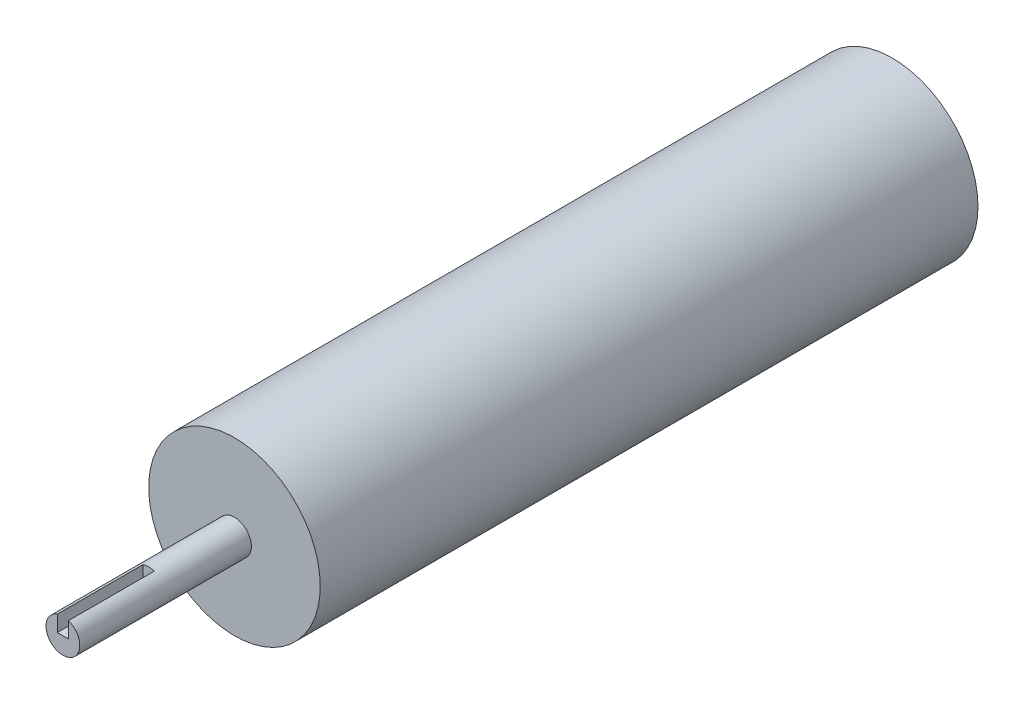
SolidWorks part; units mm, degrees
ref_plane "Front Plane" through (0, 0, 0) normal (0, 0, 1) x (1, 0, 0)
ref_plane "Top Plane" through (0, 0, 0) normal (0, 1, 0) x (1, 0, 0)
ref_plane "Right Plane" through (0, 0, 0) normal (1, 0, 0) x (0, 0, -1)
sketch "Sketch1" plane through (0, 0, 0) normal (0, 0, 1) x (1, 0, 0)
  circle A1 centre (0, 0) radius 38.1
  dimension "D2" = 76.2
extrude "Boss-Extrude1" add sketch "Sketch1" along normal blind 292.1
sketch "Sketch3" plane through (0, 0, 292.1) normal (0, 0, 1) x (1, 0, 0)
  line L0 (0, 38.1) -> (0, -38.1) construction
  line L1 (-38.1, 0) -> (38.1, 0) construction
  circle A0 centre (0, 0) radius 7.5
  circle A1 centre (0, 0) radius 38.1 construction
  dimension "D1" = 15
extrude "Boss-Extrude2" add sketch "Sketch3" along normal blind 76.2
sketch "Sketch4" plane through (0, 0, 368.3) normal (0, 0, 1) x (1, 0, 0)
  line L1 (-2.5, 0) -> (2.5, 0)
  line L2 (-2.5, 0) -> (-2.5, 7.0711)
  line L3 (2.5, 0) -> (2.5, 7.0711)
  circle A1 centre (0, 0) radius 7.5 construction
  point P10 (0, 0)
  dimension "D1" = 5
extrude "Cut-Extrude1" cut sketch "Sketch4" against normal blind 38.1 and the other way through all
sketch "Sketch5" plane through (0, 0, 0) normal (0, 0, -1) x (-1, 0, 0)
  circle A0 centre (0, 0) radius 7.5
  dimension "D1" = 15
extrude "Boss-Extrude3" add sketch "Sketch5" along normal blind 11
